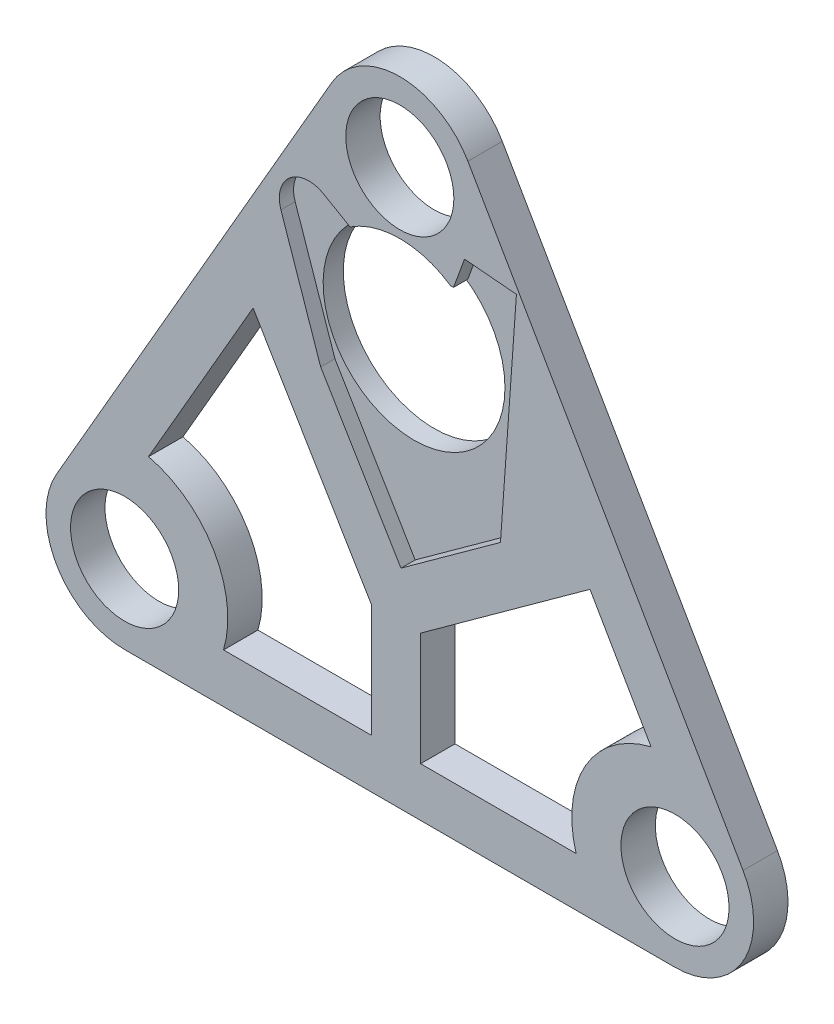
SolidWorks part; units mm, degrees
ref_plane "Front Plane" through (0, 0, 0) normal (0, 0, 1) x (1, 0, 0)
ref_plane "Top Plane" through (0, 0, 0) normal (0, 1, 0) x (1, 0, 0)
ref_plane "Right Plane" through (0, 0, 0) normal (1, 0, 0) x (0, 0, -1)
sketch "Sketch1" plane through (0, 0, 0) normal (0, 0, 1) x (1, 0, 0)
  line L0 (3.85, 0) -> (-3.85, 0) construction
  line L1 (42.1436, 104.9948) -> (-13.8564, 8)
  line L2 (69.8564, 104.9948) -> (125.8564, 8)
  line L3 (0, -16) -> (112, -16)
  circle A0 centre (0, 0) radius 11
  circle A1 centre (112, 0) radius 11
  arc A2 (-13.8564, 8) -> (0, -16) centre (0, 0) ccw
  arc A3 (112, -16) -> (125.8564, 8) centre (112, 0) ccw
  circle A4 centre (56, 96.9948) radius 11
  arc A5 (69.8564, 104.9948) -> (42.1436, 104.9948) centre (56, 96.9948) ccw
  dimension "D1" = 22
  dimension "D2" = 22
  dimension "D3" = 32
  dimension "D4" = 32
  dimension "D5" = 112
  dimension "D6" = 22
  dimension "D7" = 32
  dimension "D8" = 112
  dimension "D9" = 112
extrude "Boss-Extrude1" add sketch "Sketch1" along normal blind 7
sketch "Sketch3" plane through (0, 0, 7) normal (0, 0, 1) x (1, 0, 0)
  line L0 (56, 71.0948) -> (56, 69.0948) construction
  circle A0 centre (56, 96.9948) radius 27.9 construction
  circle A1 centre (56, 65.9448) radius 5.15 construction
  circle A2 centre (56, 65.9448) radius 18.5
  dimension "D1" = 55.8
  dimension "D2" = 10.3
  dimension "D4" = 37
  dimension "D3" = 2
extrude "Cut-Extrude1" cut sketch "Sketch3" against normal through all
sketch "Sketch4" plane through (0, 0, 7) normal (0, 0, 1) x (1, 0, 0)
  line L0 (46.11, 81.2948) -> (66.94, 81.2948)
  line L1 (66.94, 81.2948) -> (69.1631, 87.4028)
  line L2 (69.1631, 87.4028) -> (79.7352, 86.4779)
  line L3 (79.7352, 86.4779) -> (76.4824, 41.1244)
  line L4 (76.4824, 41.1244) -> (56.2308, 26.4659)
  line L5 (56.2308, 26.4659) -> (39.9013, 53.753)
  line L6 (39.9013, 53.753) -> (31.8042, 77.4054)
  line L7 (46.11, 81.2948) -> (40.4808, 84.5448)
  line L8 (56, 65.9448) -> (56, 81.2948) construction
  line L9 (56, 65.9448) -> (63.15, 65.9448) construction
  circle A0 centre (56, 65.9448) radius 7.15 construction
  arc A1 (40.4808, 84.5448) -> (31.8042, 77.4054) centre (37.4808, 79.3487) ccw
  point P12 (48.5128, 87.091)
  point P14 (0, 0)
  dimension "D1" = 14.3
  dimension "D8" = 12
  dimension "D15" = 15.35
  dimension "D2" = 85
  dimension "D3" = 130
  dimension "D4" = 168
  dimension "D5" = 105
  dimension "D6" = 250
  dimension "D7" = 210
  dimension "D9" = 25
  dimension "D10" = 31.8
  dimension "D11" = 25
  dimension "D12" = 45.47
  dimension "D13" = 6.5
  dimension "D14" = 20.83
  dimension "D16" = 90
  dimension "D17" = 9.89
  dimension "D18" = 6.5
extrude "Cut-Extrude2" cut sketch "Sketch4" against normal blind 2.9
sketch "Sketch5" plane through (0, 0, 7) normal (0, 0, 1) x (1, 0, 0)
  line L0 (26.1396, 57.2751) -> (4.8662, 20.4284)
  line L1 (42.1436, 104.9948) -> (-13.8564, 8) construction
  line L2 (20.1246, -6) -> (50.2315, -6)
  line L3 (26.1396, 57.2751) -> (50.2315, 17.017)
  line L4 (50.2315, 17.017) -> (50.2315, -6)
  line L5 (60.2315, 17.017) -> (60.2315, -6)
  line L6 (39.9013, 53.753) -> (56.2308, 26.4659) construction
  line L7 (39.9013, 53.753) -> (56.2308, 26.4659) construction
  line L8 (0, -16) -> (112, -16) construction
  line L9 (94.6994, 41.9655) -> (107.1338, 20.4284)
  line L10 (125.8564, 8) -> (69.8564, 104.9948) construction
  line L11 (94.6994, 41.9655) -> (60.2315, 17.017)
  line L12 (56.2308, 26.4659) -> (76.4824, 41.1244) construction
  line L13 (60.2315, -6) -> (91.8754, -6)
  arc A0 (20.1246, -6) -> (4.8662, 20.4284) centre (0, 0) ccw
  circle A1 centre (0, 0) radius 11 construction
  arc A2 (107.1338, 20.4284) -> (91.8754, -6) centre (112, 0) ccw
  circle A3 centre (112, 0) radius 11 construction
  point P30 (62.6156, 22.8444)
  point P33 (0, 0)
  dimension "D1" = 10
  dimension "D5" = 10
  dimension "D2" = 10
  dimension "D3" = 10
  dimension "D4" = 10
  dimension "D6" = 10
  dimension "D7" = 10
  dimension "D8" = 10
extrude "Cut-Extrude3" cut sketch "Sketch5" against normal through all
